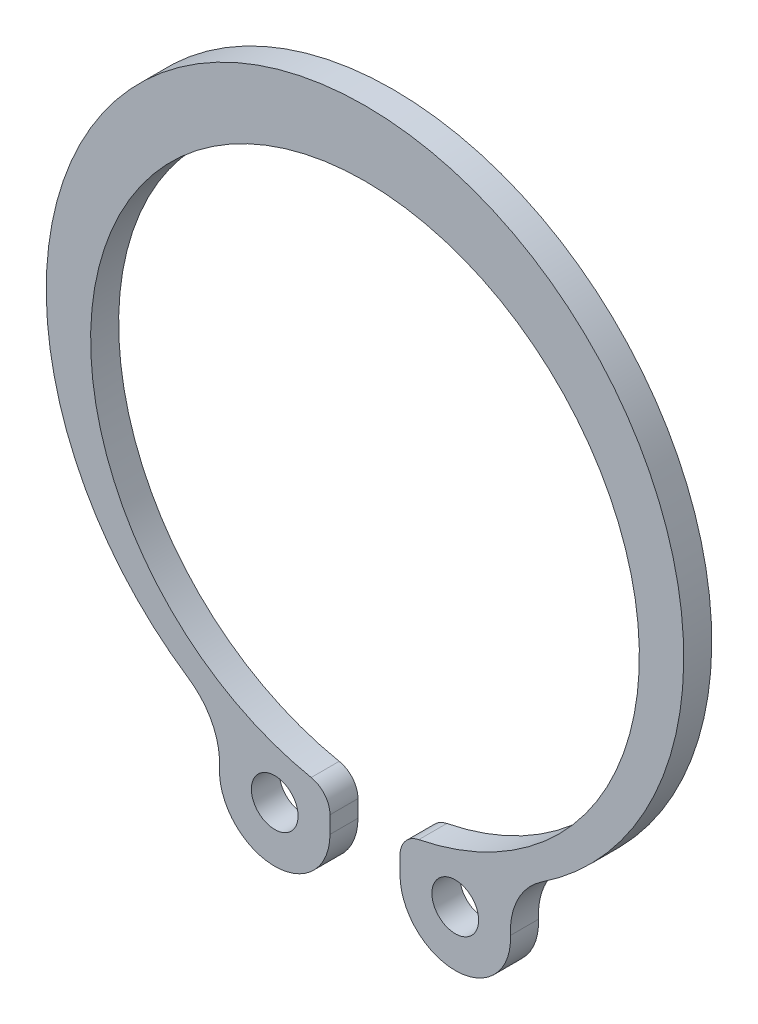
SolidWorks part; units mm, degrees
material "AISI Тип A2 Инструментальная сталь"
ref_plane "Спереди" through (0, 0, 0) normal (0, 0, 1) x (1, 0, 0)
ref_plane "Сверху" through (0, 0, 0) normal (0, 1, 0) x (1, 0, 0)
ref_plane "Справа" through (0, 0, 0) normal (1, 0, 0) x (0, 0, -1)
sketch "Эскиз1" plane through (0, 0, 0) normal (0, 0, 1) x (1, 0, 0)
  line L0 (0, -1000) -> (0, 49000) construction
  line L1 (-1.5, -14.1307) -> (-1.5, -13.4025)
  line L2 (1.5, -14.1307) -> (1.5, -13.4025)
  arc A0 (7.5631, -11.3632) -> (-7.5631, -11.3632) centre (0, 0) ccw
  arc A1 (2.3039, -12.4219) -> (-2.3039, -12.4219) centre (0, -0.9) ccw
  circle A2 centre (-3.8661, -14.1307) radius 1
  arc A3 (-6.2291, -14.0116) -> (-1.5, -14.1307) centre (-3.8661, -14.1307) ccw
  arc A4 (-2.3039, -12.4219) -> (-1.5, -13.4025) centre (-2.5, -13.4025) cw
  arc A5 (-7.5631, -11.3632) -> (-6.2291, -14.0116) centre (-9.2253, -13.8606) cw
  arc A6 (7.5631, -11.3632) -> (6.2291, -14.0116) centre (9.2253, -13.8606) ccw
  arc A7 (2.3039, -12.4219) -> (1.5, -13.4025) centre (2.5, -13.4025) ccw
  arc A8 (6.2291, -14.0116) -> (1.5, -14.1307) centre (3.8661, -14.1307) cw
  circle A9 centre (3.8661, -14.1307) radius 1
  point P17 (-1.5, -12.5539)
  dimension "D2" = 23.5
  dimension "D3" = 27.3
  dimension "D4" = 2
  dimension "r1" = 3
  dimension "r2" = 1
  dimension "e" = 0.9
  dimension "l" = 3
  dimension "a" = 4.4
extrude "Бобышка-Вытянуть1" add sketch "Эскиз1" along normal blind 1.2
